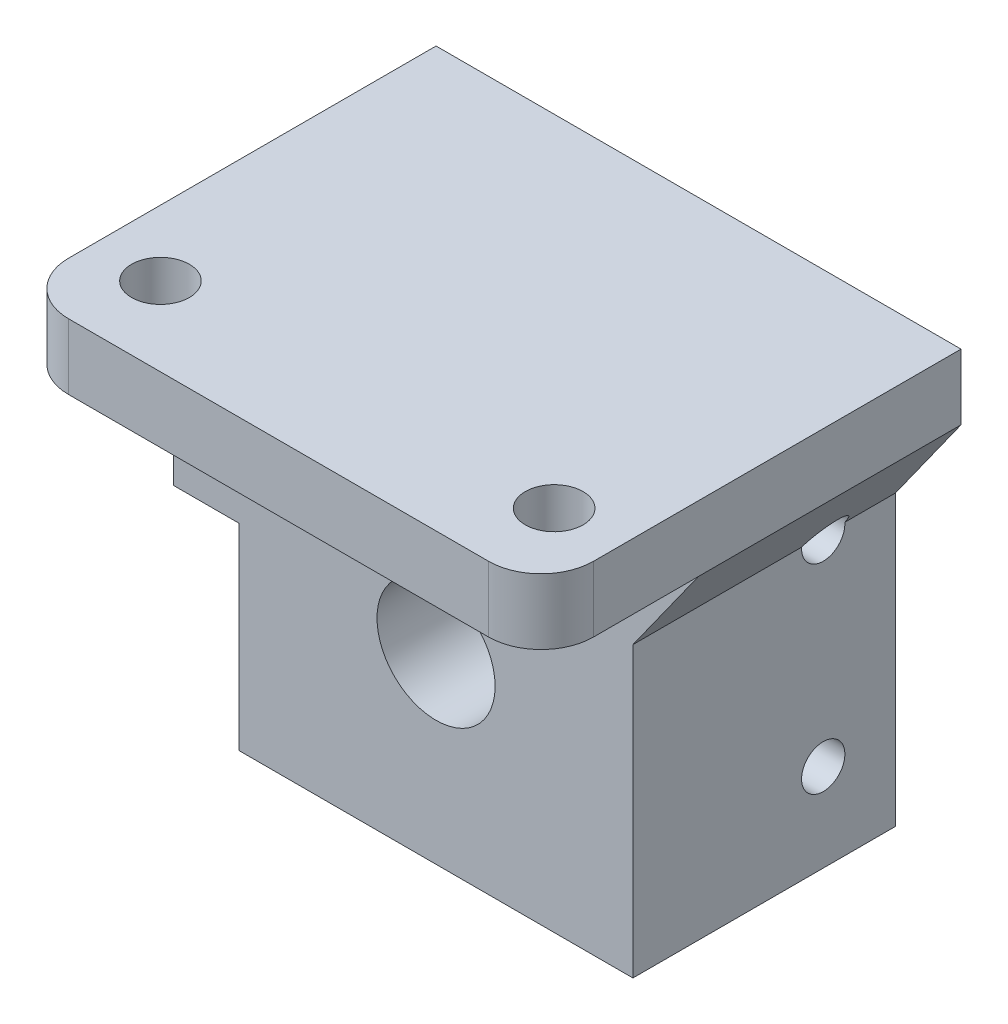
SolidWorks part; units mm, degrees
ref_plane "Plan de face" through (0, 0, 0) normal (0, 0, 1) x (1, 0, 0)
ref_plane "Plan de dessus" through (0, 0, 0) normal (0, 1, 0) x (1, 0, 0)
ref_plane "Plan de droite" through (0, 0, 0) normal (1, 0, 0) x (0, 0, -1)
sketch "Esquisse1" plane through (0, 0, 0) normal (0, 0, 1) x (1, 0, 0)
  line L1 (-20, 17) -> (20, 17)
  line L2 (-20, 17) -> (-20, -17)
  line L3 (-20, -17) -> (20, -17)
  line L4 (20, 17) -> (20, -17)
  dimension "D1" = 40
  dimension "D2" = 34
  dimension "D3" = 17
  dimension "D4" = 20
extrude "Boss.-Extru.1" add sketch "Esquisse1" along normal blind 20
sketch "Esquisse2" plane through (0, 0, 20) normal (0, 0, 1) x (1, 0, 0)
  line L1 (20, 17) -> (-20, 17)
  line L2 (20, 17) -> (20, 12)
  line L3 (20, 12) -> (-20, 12)
  line L4 (-20, 17) -> (-20, 12)
  line L5 (-20, 17) -> (-20, -17) construction
  dimension "D1" = 5
extrude "Boss.-Extru.3" add sketch "Esquisse2" along normal blind 20
sketch "Esquisse4" plane through (0, 0, 20) normal (0, 0, 1) x (1, 0, 0)
  line L0 (20, -17) -> (20, 12) construction
  line L1 (-20, -17) -> (20, -17) construction
  circle A0 centre (0, -3) radius 4.5
  dimension "D1" = 9
  dimension "D2" = 20
  dimension "D3" = 14
extrude "Enlèv. mat.-Extru.1" cut sketch "Esquisse4" against normal through all
sketch "Esquisse5" plane through (0, 0, 0) normal (0, 0, -1) x (-1, 0, 0)
  circle A0 centre (0, -3) radius 8.1
  dimension "D1" = 16.2
extrude "Enlèv. mat.-Extru.2" cut sketch "Esquisse5" against normal blind 12
sketch "Esquisse6" plane through (0, 0, 20) normal (0, 0, 1) x (1, 0, 0)
  line L0 (-20, -17) -> (-20, -2)
  line L1 (-15, -7) -> (-15, -17)
  line L2 (-20, -17) -> (20, -17) construction
  line L3 (-15, -17) -> (-20, -17)
  line L4 (-20, 12) -> (-20, -17) construction
  line L5 (20, 12) -> (15, 5)
  line L6 (15, 5) -> (15, -17)
  line L7 (15, -17) -> (20, -17)
  line L8 (20, -17) -> (20, 12)
  line L10 (-20, -2) -> (-15, -2)
  line L11 (-15, -2) -> (-15, -7)
  dimension "D1" = 5
  dimension "D2" = 30
  dimension "D3" = 10
  dimension "D4" = 22
  dimension "D5" = 15
extrude "Enlèv. mat.-Extru.3" cut sketch "Esquisse6" against normal through all
sketch "Esquisse8" plane through (0, 12, 0) normal (0, -1, 0) x (1, 0, 0)
  line L0 (-20, 40) -> (20, 40) construction
  line L1 (-20, 40) -> (-20, 20) construction
  circle A0 centre (-15, 26) radius 2.2
  circle A1 centre (15, 26) radius 2.2
  dimension "D2" = 4.4
  dimension "D3" = 4.4
  dimension "D1" = 30
  dimension "D4" = 14
  dimension "D5" = 5
  dimension "D6" = 14
extrude "Enlèv. mat.-Extru.5" cut sketch "Esquisse8" against normal through all
sketch "Esquisse10" plane through (0, 0, 12) normal (0, 0, -1) x (-1, 0, 0)
  circle A0 centre (0, -3) radius 4.5
extrude "Boss.-Extru.4" add sketch "Esquisse10" against normal blind 1
sketch "Esquisse11" plane through (0, 12, 0) normal (0, -1, 0) x (1, 0, 0)
  line L0 (20, 40) -> (20, 20) construction
  line L1 (-20, 40) -> (20, 40)
  line L2 (-20, 40) -> (-20, 32)
  line L3 (-20, 32) -> (20, 32)
  line L4 (20, 40) -> (20, 32)
  dimension "D1" = 8
extrude "Enlèv. mat.-Extru.6" cut sketch "Esquisse11" against normal through all
fillet "Congé6" radius 4 2 edges at (-20, 14.5, 32) (20, 14.5, 32)
sketch "Esquisse15" plane through (0, 0, 0) normal (0, 0, -1) x (-1, 0, 0)
  line L0 (0, -11.1) -> (-15, -11.1) construction
  line L1 (-15, 5) -> (-15, -17) construction
  circle A0 centre (0, -3) radius 8.1 construction
sketch "Esquisse14" plane through (15, 0, 0) normal (1, 0, 0) x (0, 0, -1)
  line L0 (-12, -11.1) -> (-12, 5.1) construction
  line L1 (0, -11.1) -> (-20, -11.1) construction
  line L2 (-20, 5) -> (-20, -17) construction
  circle A0 centre (-5.5, -10.3) radius 1.65
  circle A1 centre (-5.5, 4.9) radius 1.65
  dimension "D1" = 3.3
  dimension "D2" = 3.3
  dimension "D3" = 15.2
  dimension "D4" = 6.5
  dimension "D5" = 6.5
  dimension "D6" = 16
extrude "Enlèv. mat.-Extru.7" cut sketch "Esquisse14" against normal through all and the other way through all
